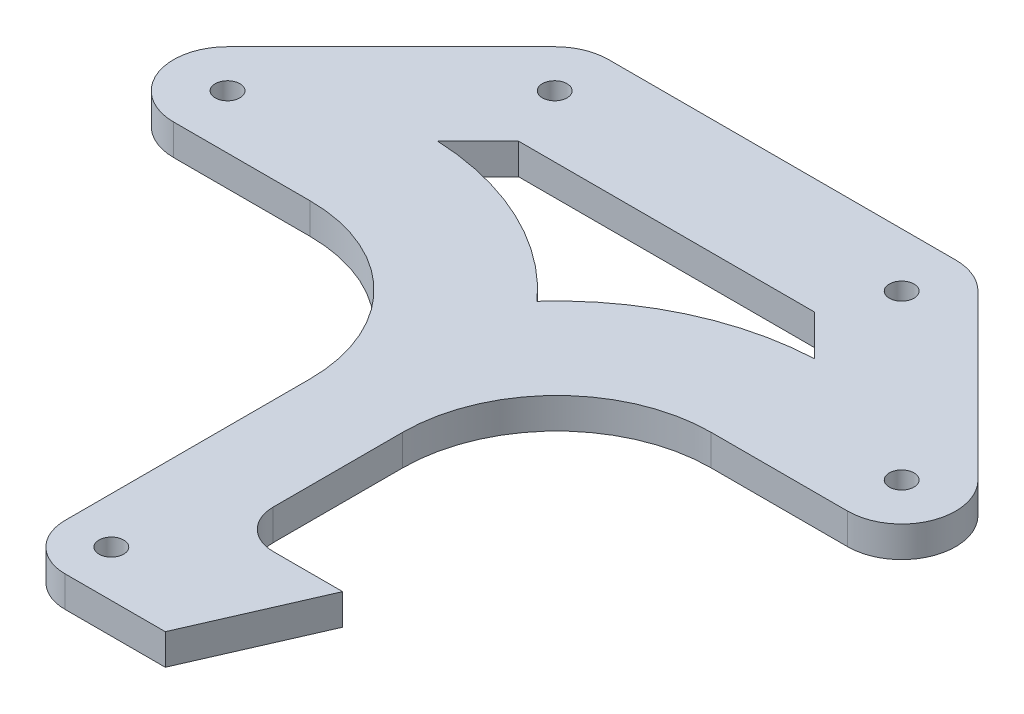
SolidWorks part; units mm, degrees
ref_plane "Front Plane" through (0, 0, 0) normal (0, 0, 1) x (1, 0, 0)
ref_plane "Top Plane" through (0, 0, 0) normal (0, 1, 0) x (1, 0, 0)
ref_plane "Right Plane" through (0, 0, 0) normal (1, 0, 0) x (0, 0, -1)
sketch "Sketch1" plane through (0, 0, 0) normal (0, 1, 0) x (1, 0, 0)
  line L0 (-22.5, 80) -> (-43.7132, 58.7868) construction
  line L1 (-10, 0) -> (10, 0) construction
  line L2 (-10, 0) -> (-10, 80) construction
  line L3 (-10, 80) -> (10, 80) construction
  line L4 (10, 0) -> (10, 80) construction
  line L5 (0, 80) -> (0, 0) construction
  line L6 (-10, 40) -> (10, 40) construction
  line L7 (-22.5, 80) -> (22.5, 80) construction
  line L8 (-6, 0) -> (6, 0) construction
  line L9 (-6, 0) -> (-6, 80) construction
  line L10 (-6, 80) -> (6, 80) construction
  line L11 (6, 0) -> (6, 80) construction
  line L12 (0, 80) -> (0, 0) construction
  line L13 (-6, 40) -> (6, 40) construction
  line L14 (-22.5, 87) -> (22.5, 87) construction
  line L15 (-22.5, 73) -> (22.5, 73) construction
  line L16 (-22.5, 80) -> (-43.7132, 58.7868) construction
  line L17 (-17.5503, 75.0503) -> (-38.7635, 53.837) construction
  line L18 (-27.4497, 84.9497) -> (-48.663, 63.7365) construction
  line L19 (-43.7132, 51.7868) -> (-26, 51.7868)
  line L20 (-6, 31.7868) -> (-6, 0)
  line L21 (6, 0) -> (6, 31.7868) construction
  line L22 (26, 51.7868) -> (43.7132, 51.7868)
  line L23 (-48.663, 63.7365) -> (-27.4497, 84.9497)
  line L24 (-22.5, 87) -> (22.5, 87)
  line L25 (48.663, 63.7365) -> (27.4497, 84.9497)
  line L26 (-19.1863, 72) -> (19.1863, 72)
  line L27 (24.4345, 66.7518) -> (19.1863, 72)
  line L28 (24.4345, 66.7518) -> (24.4345, 66.7518)
  line L29 (0, 55.2175) -> (0, 55.2175)
  line L30 (0, 55.2175) -> (0, 55.2175)
  line L31 (-24.4345, 66.7518) -> (-24.4345, 66.7518)
  line L32 (-24.4345, 66.7518) -> (-19.1863, 72)
  line L33 (0, 10) -> (20, 10) construction
  line L34 (11, 10) -> (20, 10)
  line L35 (20, 10) -> (13, -6)
  line L36 (13, -6) -> (0, -6)
  line L37 (6, 31.7868) -> (6, 15)
  circle A4 centre (0, 0) radius 10 construction
  circle A5 centre (-22.5, 80) radius 20 construction
  circle A6 centre (-43.7132, 58.7868) radius 10 construction
  circle A7 centre (43.7132, 58.7868) radius 10 construction
  circle A8 centre (22.5, 80) radius 20 construction
  circle A9 centre (-22.5, 80) radius 3
  circle A10 centre (22.5, 80) radius 3
  circle A11 centre (0, 0) radius 3
  circle A12 centre (-43.7132, 58.7868) radius 3
  circle A13 centre (43.7132, 58.7868) radius 3
  arc A14 (-22.5, 87) -> (-22.5, 73) centre (-22.5, 80) ccw construction
  arc A15 (22.5, 73) -> (22.5, 87) centre (22.5, 80) ccw construction
  arc A16 (-17.5503, 75.0503) -> (-27.4497, 84.9497) centre (-22.5, 80) ccw construction
  arc A17 (-48.663, 63.7365) -> (-38.7635, 53.837) centre (-43.7132, 58.7868) ccw construction
  arc A18 (-6, 0) -> (6, 0) centre (0, 0) ccw construction
  arc A19 (-43.7132, 51.7868) -> (-48.663, 63.7365) centre (-43.7132, 58.7868) cw
  arc A20 (-27.4497, 84.9497) -> (-22.5, 87) centre (-22.5, 80) cw
  arc A21 (27.4497, 84.9497) -> (22.5, 87) centre (22.5, 80) ccw
  arc A22 (43.7132, 51.7868) -> (48.663, 63.7365) centre (43.7132, 58.7868) ccw
  arc A23 (26, 51.7868) -> (6, 31.7868) centre (26, 31.7868) ccw
  arc A24 (-6, 31.7868) -> (-26, 51.7868) centre (-26, 31.7868) ccw
  arc A25 (19.1863, 72) -> (19.1863, 72) centre (19.1863, 72) ccw
  arc A26 (24.4345, 66.7518) -> (24.4345, 66.7518) centre (24.4345, 66.7518) ccw
  arc A27 (24.4345, 66.7518) -> (0, 55.2175) centre (26, 31.7868) ccw
  arc A28 (0, 55.2175) -> (0, 55.2175) centre (0, 55.2175) cw
  arc A29 (0, 55.2175) -> (-24.4345, 66.7518) centre (-26, 31.7868) ccw
  arc A30 (-24.4345, 66.7518) -> (-24.4345, 66.7518) centre (-24.4345, 66.7518) cw
  arc A31 (-19.1863, 72) -> (-19.1863, 72) centre (-19.1863, 72) cw
  arc A32 (-6, 0) -> (0, -6) centre (0, 0) ccw
  arc A33 (11, 10) -> (6, 15) centre (11, 15) cw
  circle A35 centre (0, 0) radius 1.6
  circle A36 centre (43.7132, 58.7868) radius 1.6
  circle A37 centre (22.5, 80) radius 1.6
  circle A38 centre (-22.5, 80) radius 1.6
  circle A39 centre (-43.7132, 58.7868) radius 1.6
  point P20 (0, 40)
  point P24 (0, 80)
  point P30 (-33.1066, 69.3934)
  point P47 (0, 87)
  point P52 (6, 51.7868)
  point P55 (-6, 51.7868)
  point P85 (6, 10)
  point P91 (0, 0)
  point P532 (0, 40)
  dimension "D1" = 20
  dimension "D2" = 80
  dimension "D6" = 135
  dimension "D7" = 20
  dimension "D4" = 40
  dimension "D8" = 3.2
  dimension "D9" = 6
  dimension "D14" = 7
  dimension "D15" = 7
  dimension "D16" = 20
  dimension "D20" = 5
  dimension "D3" = 20
  dimension "D5" = 12.5
  dimension "D13" = 12
  dimension "D18" = 20
  dimension "D19" = 13
  dimension "D17" = 15
extrude "Boss-Extrude1" add sketch "Sketch1" along normal blind 4 contours L34 A33 L37 A23 L22 A22 L25 A21 L24 A20 L23 A19 L19 A24 L20 A32 L36 L35 A27 A29 L32 L26 L27 A9 A10 A11 A12 A13 | A11 A35 | A13 A36 | A10 A37 | A9 A38 | A12 A39
